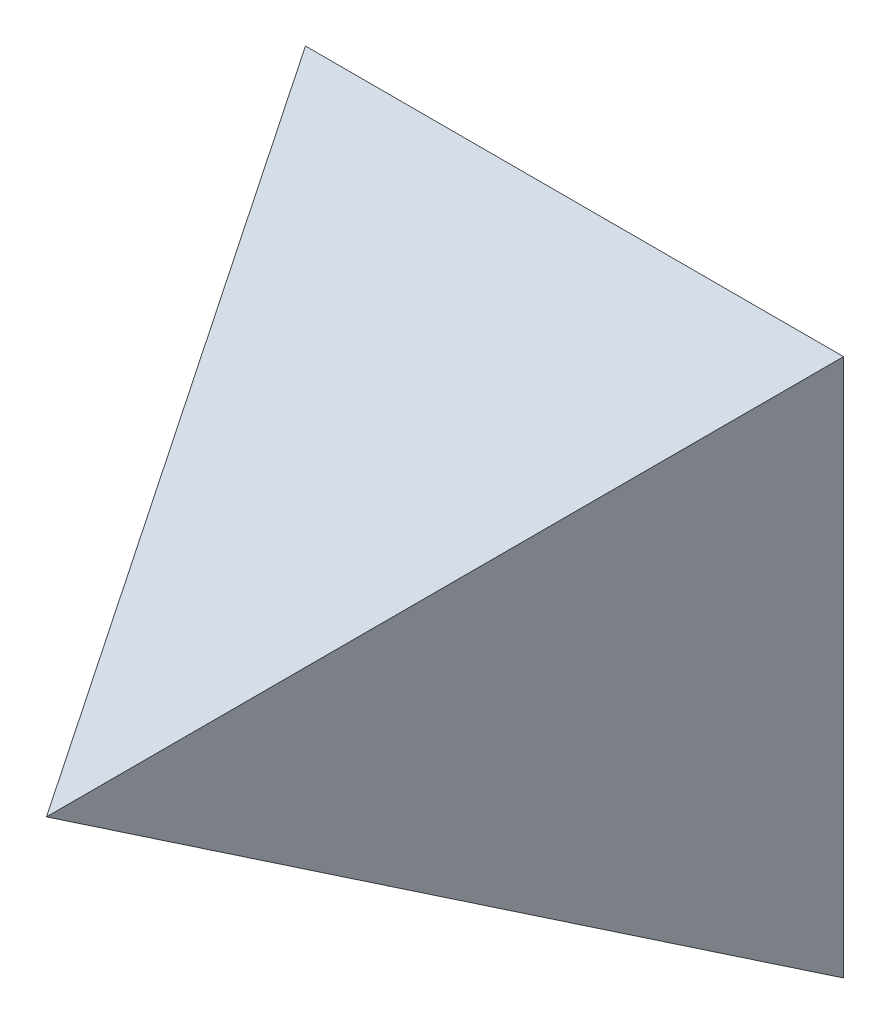
SolidWorks part; units mm, degrees
ref_plane "Front Plane" through (0, 0, 0) normal (0, 0, 1) x (1, 0, 0)
ref_plane "Top Plane" through (0, 0, 0) normal (0, 1, 0) x (1, 0, 0)
ref_plane "Right Plane" through (0, 0, 0) normal (1, 0, 0) x (0, 0, -1)
sketch "Sketch3" plane through (0, 0, 0) normal (0, 0, 1) x (1, 0, 0)
  line L1 (-16.4331, 10) -> (-6.4331, 10)
  line L2 (-16.4331, 10) -> (-16.4331, 0)
  line L3 (-16.4331, 0) -> (-6.4331, 0)
  line L4 (-6.4331, 10) -> (-6.4331, 0)
  dimension "D1" = 10
  dimension "D2" = 10
extrude "Boss-Extrude1" add sketch "Sketch3" along normal blind 10 draft 27
